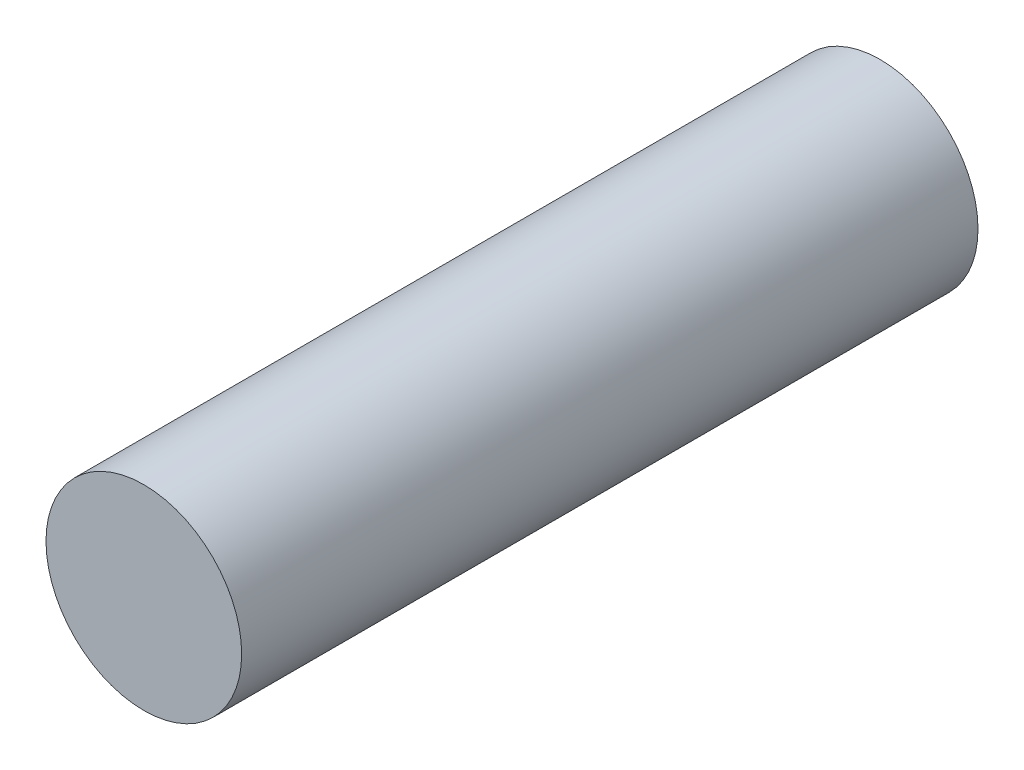
SolidWorks part; units mm, degrees
material "Hierro dúctil"
ref_plane "Alzado" through (0, 0, 0) normal (0, 0, 1) x (1, 0, 0)
ref_plane "Planta" through (0, 0, 0) normal (0, 1, 0) x (1, 0, 0)
ref_plane "Vista lateral" through (0, 0, 0) normal (1, 0, 0) x (0, 0, -1)
sketch "Croquis1" plane through (0, 0, 0) normal (0, 0, 1) x (1, 0, 0)
  circle A0 centre (0, 0) radius 4.65
  dimension "D1" = 9.3
extrude "Saliente-Extruir1" add sketch "Croquis1" along normal blind 35
